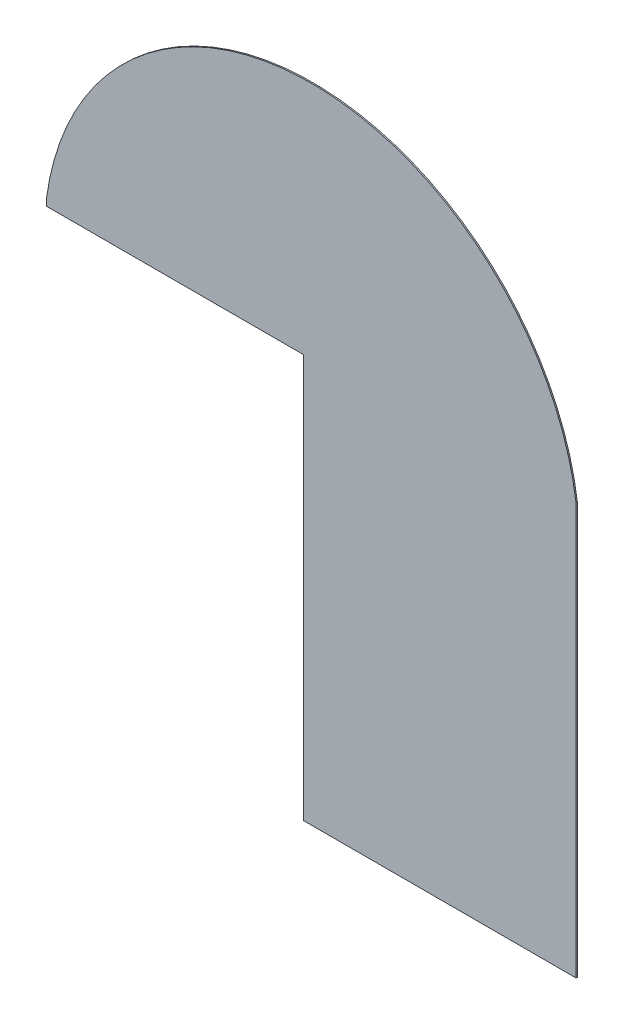
SolidWorks part; units mm, degrees
ref_plane "Front Plane" through (0, 0, 0) normal (0, 0, 1) x (1, 0, 0)
ref_plane "Top Plane" through (0, 0, 0) normal (0, 1, 0) x (1, 0, 0)
ref_plane "Right Plane" through (0, 0, 0) normal (1, 0, 0) x (0, 0, -1)
sketch "Sketch1" plane through (0, 0, 0) normal (0, 0, 1) x (1, 0, 0)
  line L2 (1030, 800) -> (1030, -800)
  line L3 (1030, -800) -> (-1030, -800)
  line L4 (-1030, 800) -> (-1030, -800)
  line L5 (1030, 800) -> (-1030, -800) construction
  line L6 (1030, -800) -> (-1030, 800) construction
  arc A1 (-1030, 800) -> (1030, 800) centre (0, 660.6111) cw
  point P0 (0, 0)
  point P1 (0, 0)
  point P10 (0, 1700)
  dimension "D1" = 2060
  dimension "D2" = 900
  dimension "D3" = 1600
extrude "Boss-Extrude1" add sketch "Sketch1" along normal mid plane 5
sketch "Sketch2" plane through (0, 0, 2.5) normal (0, 0, 1) x (1, 0, 0)
  line L0 (-1030, 800) -> (-30, 800)
  line L1 (-30, 800) -> (-30, -800)
  line L2 (-1030, -800) -> (1030, -800) construction
  line L3 (-1030, 800) -> (-1030, -800)
  line L4 (-1030, -800) -> (1030, -800)
  line L5 (1030, -800) -> (1030, 800)
  line L6 (-1030, 800) -> (-1030, -800)
  line L7 (-1030, -800) -> (1030, -800)
  line L8 (1030, -800) -> (1030, 800) construction
  line L9 (-1030, 770) -> (-30, 770)
  arc A1 (1030, 800) -> (-1030, 800) centre (0, 660.6111) ccw
  arc A2 (1030, 800) -> (-1030, 800) centre (0, 660.6111) ccw construction
  line M8 (-1030, -800) -> (1030, -800)
  dimension "D2" = 1000
  dimension "D3" = 30
  dimension "D1" = 0
extrude "Cut-Extrude2" cut sketch "Sketch2" against normal through all contours L9 L6 L1 M8
